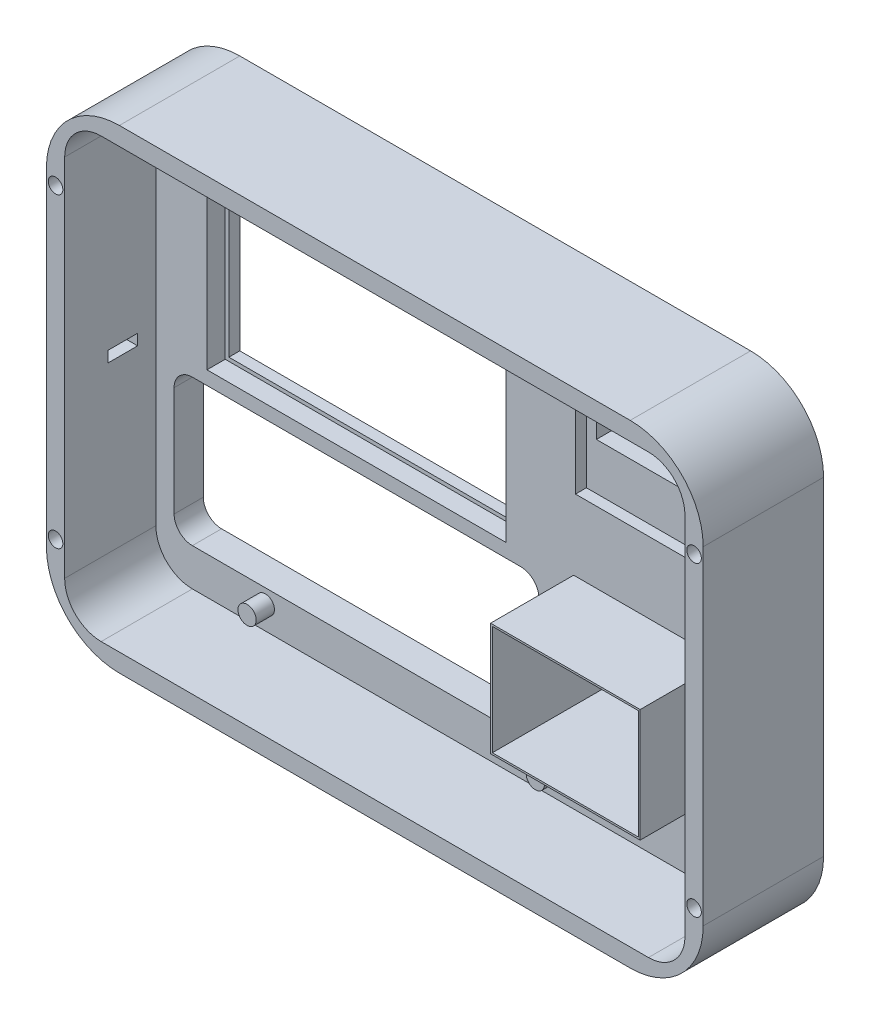
SolidWorks part; units mm, degrees
ref_plane "Front Plane" through (0, 0, 0) normal (0, 0, 1) x (1, 0, 0)
ref_plane "Top Plane" through (0, 0, 0) normal (0, 1, 0) x (1, 0, 0)
ref_plane "Right Plane" through (0, 0, 0) normal (1, 0, 0) x (0, 0, -1)
sketch "Sketch2" plane through (0, 0, 0) normal (0, 0, 1) x (1, 0, 0)
  line L0 (-96.4836, 54.7324) -> (-96.4836, -35.2676)
  line L1 (-76.4836, -55.2676) -> (63.5164, -55.2676)
  line L2 (83.5164, -35.2676) -> (83.5164, 54.7324)
  line L3 (63.5164, 74.7324) -> (-76.4836, 74.7324)
  line L4 (-76.4836, 54.7324) -> (-76.4836, 4.7324)
  line L7 (3.5164, 54.7324) -> (-76.4836, 54.7324)
  line L8 (23.5164, 4.7324) -> (23.5164, -25.2676)
  line L9 (23.5164, -25.2676) -> (63.5164, -25.2676)
  line L10 (63.5164, -25.2676) -> (63.5164, 4.7324)
  line L13 (3.5164, 4.7324) -> (-76.4836, 4.7324)
  line L15 (3.5164, 4.7324) -> (3.5164, 54.7324)
  line L77 (23.5164, -25.2676) -> (23.5164, -55.2676)
  line L79 (60.7864, 47.5695) -> (26.2464, 47.5695)
  line L80 (26.2464, 52.5695) -> (60.7864, 52.5695)
  line L81 (26.2464, 52.5695) -> (26.2464, 47.5695)
  line L83 (60.7864, 52.5695) -> (60.7864, 47.5695)
  line L85 (60.7864, 42.5695) -> (26.2464, 42.5695)
  line L86 (60.7864, 37.5695) -> (26.2464, 37.5695)
  line L87 (26.2464, 42.5695) -> (26.2464, 37.5695)
  line L90 (60.7864, 42.5695) -> (60.7864, 37.5695)
  line L91 (-86.4836, -10) -> (13.5164, -10)
  line L92 (-81.4836, 0) -> (8.5164, 0)
  line L93 (-86.4836, -5) -> (-86.4836, -35)
  line L94 (-81.4836, -40) -> (8.5164, -40)
  line L95 (13.5164, -5) -> (13.5164, -35)
  line L96 (13.5164, -20) -> (-86.4836, -20)
  line L97 (-86.4836, -30) -> (13.5164, -30)
  line L98 (-61.4836, 0) -> (-61.4836, -40)
  line L99 (-36.4836, 0) -> (-36.4836, -40)
  line L100 (-11.4836, 0) -> (-11.4836, -40)
  line L101 (23.5164, 4.7324) -> (23.5164, 74.7324)
  line L102 (23.5164, -25.2676) -> (23.5164, -55.2676)
  line L103 (63.5164, 4.7324) -> (23.5164, 4.7324)
  line L104 (63.5164, 74.7324) -> (63.5164, -55.2676)
  line L105 (43.5164, 65.8881) -> (23.5164, 65.8881)
  line L106 (43.5164, 65.8881) -> (63.5164, 65.8881)
  line L107 (63.5164, 25.8881) -> (23.5164, 25.8881)
  arc A0 (-96.4836, -35.2676) -> (-76.4836, -55.2676) centre (-76.4836, -35.2676) ccw
  arc A1 (63.5164, -55.2676) -> (83.5164, -35.2676) centre (63.5164, -35.2676) ccw
  arc A2 (83.5164, 54.7324) -> (63.5164, 74.7324) centre (63.5164, 54.7324) ccw
  arc A3 (-96.4836, 54.7324) -> (-76.4836, 74.7324) centre (-76.4836, 54.7324) cw
  arc A70 (8.5164, -40) -> (13.5164, -35) centre (8.5164, -35) ccw
  arc A71 (8.5164, 0) -> (13.5164, -5) centre (8.5164, -5) cw
  arc A72 (-86.4836, -35) -> (-81.4836, -40) centre (-81.4836, -35) ccw
  arc A73 (-81.4836, 0) -> (-86.4836, -5) centre (-81.4836, -5) ccw
  circle A74 centre (43.5164, 45.8881) radius 20
  point P6 (-96.4836, -55.2676)
  point P9 (83.5164, -55.2676)
  point P12 (83.5164, 74.7324)
  point P27 (13.5164, 0)
  point P31 (-86.4836, -40)
  point P35 (-86.4836, 0)
  dimension "D3" = 80
  dimension "D10" = 40
  dimension "D12" = 5
  dimension "D14" = 2.73
  dimension "D21" = 40
  dimension "D1" = 180
  dimension "D2" = 130
  dimension "D4" = 40
  dimension "D5" = 30
  dimension "D6" = 30
  dimension "D7" = 20
  dimension "D8" = 50
  dimension "D9" = 10
  dimension "D11" = 10
  dimension "D13" = 100
  dimension "D15" = 120
  dimension "D16" = 20
  dimension "D17" = 2.73
  dimension "D18" = 34.54
  dimension "D19" = 40
  dimension "D20" = 5
  dimension "D22" = 40
  dimension "D23" = 5
  dimension "2" = 25
extrude "Boss-Extrude5" add sketch "Sketch2" along normal blind 33 contours L2 A2 L104 L10 A1 | L105 L106 L104 L3 L101 | A74 L104 L106 | A74 L105 L101 | A74 L101 L107 | A74 L107 L104 | A74 L80 L83 L79 L81 L85 L90 L86 L87 | L104 L107 L101 L103 | L104 L9 L77 L1 | A3 L0 A0 L1 L77 L8 L101 L3 A73 L92 A71 L95 A70 L94 A72 L93 L15 L13 L4 L7
sketch "Sketch4" plane through (0, 0, 33) normal (0, 0, 1) x (1, 0, 0)
  line L0 (-76.4836, -55.2676) -> (63.5164, -55.2676) construction
  line L1 (-81.4836, 69.7324) -> (68.5164, 69.7324)
  line L2 (-91.4836, 59.7324) -> (-91.4836, -40.2676)
  line L3 (-81.4836, -50.2676) -> (68.5164, -50.2676)
  line L4 (78.5164, 59.7324) -> (78.5164, -40.2676)
  line L5 (-96.4836, 54.7324) -> (-96.4836, -35.2676) construction
  arc A0 (68.5164, 69.7324) -> (78.5164, 59.7324) centre (68.5164, 59.7324) cw
  arc A1 (68.5164, -50.2676) -> (78.5164, -40.2676) centre (68.5164, -40.2676) ccw
  arc A2 (-91.4836, -40.2676) -> (-81.4836, -50.2676) centre (-81.4836, -40.2676) ccw
  arc A3 (-81.4836, 69.7324) -> (-91.4836, 59.7324) centre (-81.4836, 59.7324) ccw
  point P12 (78.5164, -50.2676)
  point P15 (-91.4836, -50.2676)
  point P18 (-91.4836, 69.7324)
  dimension "D5" = 10
  dimension "D1" = 120
  dimension "D2" = 170
  dimension "D3" = 5
  dimension "D4" = 5
extrude "Cut-Extrude1" cut sketch "Sketch4" against normal blind 25
sketch "Sketch5" plane through (0, 0, 8) normal (0, 0, 1) x (1, 0, 0)
  line L0 (23.5164, 24.7324) -> (23.5164, 64.7324)
  line L1 (63.5164, 24.7324) -> (63.5164, 64.7324)
  line L2 (23.5164, 64.7324) -> (63.5164, 64.7324)
  line L3 (23.5164, 24.7324) -> (63.5164, 24.7324)
  line L6 (23.5164, 4.7324) -> (63.5164, 4.7324) construction
  dimension "D1" = 40
  dimension "D2" = 40
  dimension "D3" = 20
extrude "Cut-Extrude2" cut sketch "Sketch5" against normal blind 3
sketch "Sketch6" plane through (0, 0, 8) normal (0, 0, 1) x (1, 0, 0)
  line L0 (23.5164, 4.7324) -> (63.5164, 4.7324) construction
  line L1 (23.0164, 5.2324) -> (64.0164, 5.2324)
  line L2 (23.0164, 5.2324) -> (23.0164, -25.7676)
  line L3 (23.0164, -25.7676) -> (64.0164, -25.7676)
  line L4 (64.0164, 5.2324) -> (64.0164, -25.7676)
  line L5 (23.5164, -25.2676) -> (23.5164, 4.7324) construction
  line L6 (63.5164, -25.2676) -> (23.5164, -25.2676) construction
  line L7 (63.5164, -25.2676) -> (63.5164, 4.7324) construction
  line L8 (23.5164, 4.7324) -> (23.5164, -25.2676)
  line L9 (23.5164, -25.2676) -> (63.5164, -25.2676)
  line L10 (63.5164, -25.2676) -> (63.5164, 4.7324)
  line L11 (63.5164, 4.7324) -> (23.5164, 4.7324)
  dimension "D1" = 0.5
  dimension "D2" = 0.5
  dimension "D3" = 0.5
  dimension "D4" = 0.5
extrude "Boss-Extrude6" add sketch "Sketch6" along normal blind 30
sketch "Sketch7" plane through (0, 0, 8) normal (0, 0, 1) x (1, 0, 0)
  line L0 (-76.4836, 4.7324) -> (-76.4836, 54.7324) construction
  line L1 (-77.4836, 55.7324) -> (4.5164, 55.7324)
  line L2 (-77.4836, 55.7324) -> (-77.4836, 3.7324)
  line L3 (-77.4836, 3.7324) -> (4.5164, 3.7324)
  line L4 (4.5164, 55.7324) -> (4.5164, 3.7324)
  line L5 (-76.4836, 54.7324) -> (3.5164, 54.7324) construction
  line L6 (3.5164, 54.7324) -> (3.5164, 4.7324) construction
  line L7 (-76.4836, 4.7324) -> (3.5164, 4.7324) construction
  line L8 (-76.4836, 54.7324) -> (-76.4836, 4.7324)
  line L9 (-76.4836, 4.7324) -> (3.5164, 4.7324)
  line L10 (3.5164, 4.7324) -> (3.5164, 54.7324)
  line L11 (3.5164, 54.7324) -> (-76.4836, 54.7324)
  dimension "D1" = 1
  dimension "D2" = 1
  dimension "D3" = 1
  dimension "D4" = 1
extrude "Cut-Extrude3" cut sketch "Sketch7" against normal blind 5
sketch "Sketch8" plane through (0, 0, 8) normal (0, 0, 1) x (1, 0, 0)
  line L0 (-91.4836, 59.7324) -> (-91.4836, -40.2676) construction
  line L4 (68.5164, 69.7324) -> (-81.4836, 69.7324) construction
  line L5 (78.5164, -40.2676) -> (78.5164, 59.7324) construction
  line L6 (68.5164, 69.7324) -> (-81.4836, 69.7324) construction
  line L7 (-81.4836, -50.2676) -> (68.5164, -50.2676) construction
  line L8 (-81.4836, -50.2676) -> (68.5164, -50.2676) construction
  line L9 (-91.4836, 59.7324) -> (-91.4836, -40.2676) construction
  line L10 (78.5164, -40.2676) -> (78.5164, 59.7324) construction
  circle A0 centre (-77.4836, 65.7324) radius 2.5
  circle A1 centre (17.5164, 65.7324) radius 2.5
  circle A2 centre (-61.4836, -43.9476) radius 2.5
  circle A3 centre (17.5164, -43.4476) radius 2.5
  dimension "D1" = 5
  dimension "D4" = 5
  dimension "D7" = 5
  dimension "D8" = 5
  dimension "D2" = 14
  dimension "D3" = 4
  dimension "D5" = 61
  dimension "D6" = 4
  dimension "D9" = 6.32
  dimension "D10" = 6.82
  dimension "D11" = 30
  dimension "D12" = 61
extrude "Boss-Extrude7" add sketch "Sketch8" along normal blind 5
sketch "Sketch9" plane through (-96.4836, 0, 0) normal (-1, 0, 0) x (0, 0, 1)
  line L0 (0, 54.7324) -> (0, -35.2676) construction
  line L1 (21.06, 4.9182) -> (13, 4.9182)
  line L2 (21.06, 4.9182) -> (21.06, 7.9182)
  line L3 (21.06, 7.9182) -> (13, 7.9182)
  line L4 (13, 4.9182) -> (13, 7.9182)
  dimension "D1" = 8.06
  dimension "D2" = 3
  dimension "D3" = 13
  dimension "D4" = 21.06
sketch "Sketch10" plane through (23.0164, 0, 0) normal (-1, 0, 0) x (0, 0, 1)
  line L0 (38, 5.2324) -> (8, 5.2324) construction
  line L1 (30.7762, 5.2324) -> (38, 5.2324)
  line L2 (30.7762, 5.2324) -> (30.7762, -25.7676)
  line L3 (30.7762, -25.7676) -> (38, -25.7676)
  line L4 (38, 5.2324) -> (38, -25.7676)
  line L5 (38, 5.2324) -> (38, -25.7676) construction
extrude "Cut-Extrude6" cut sketch "Sketch10" against normal blind 41
sketch "Sketch14" plane through (0, 0, 33) normal (0, 0, 1) x (1, 0, 0)
  line L0 (-91.4836, 59.7324) -> (-91.4836, -40.2676) construction
  line L1 (83.5164, -35.2676) -> (83.5164, 54.7324) construction
  line L2 (63.5164, 74.7324) -> (-76.4836, 74.7324) construction
  line L3 (-76.4836, -55.2676) -> (63.5164, -55.2676) construction
  circle A0 centre (-93.9836, 51.7324) radius 2
  circle A1 centre (81.0164, 51.7324) radius 2
  circle A2 centre (81.0164, -32.2676) radius 2
  circle A3 centre (-93.9836, -32.2676) radius 2
  dimension "D1" = 4
  dimension "D2" = 4
  dimension "D3" = 4
  dimension "D4" = 4
  dimension "D5" = 2.5
  dimension "D6" = 2.5
  dimension "D7" = 2.5
  dimension "D8" = 2.5
  dimension "D9" = 23
  dimension "D10" = 23
  dimension "D11" = 23
  dimension "D12" = 23
extrude "Cut-Extrude9" cut sketch "Sketch14" against normal blind 20
extrude "Cut-Extrude11" cut sketch "Sketch9" against normal blind 5
